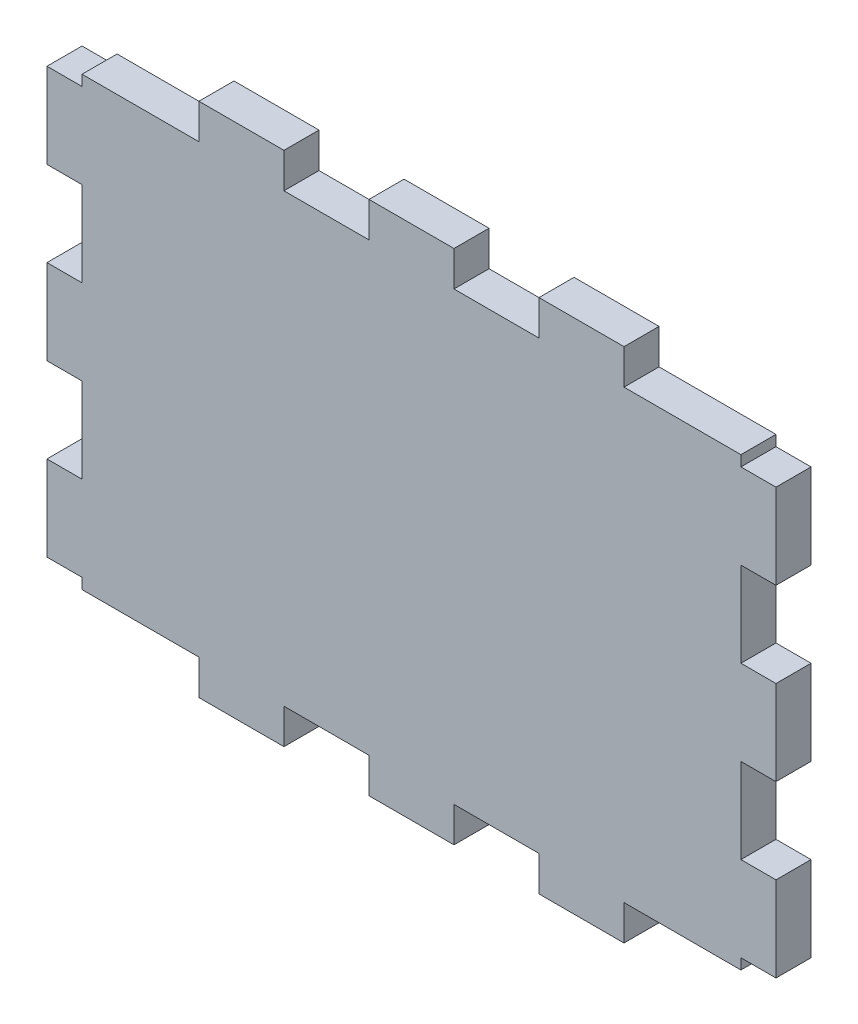
SolidWorks part; units mm, degrees
ref_plane "Plan de face" through (0, 0, 0) normal (0, 0, 1) x (1, 0, 0)
ref_plane "Plan de dessus" through (0, 0, 0) normal (0, 1, 0) x (1, 0, 0)
ref_plane "Plan de droite" through (0, 0, 0) normal (1, 0, 0) x (0, 0, -1)
sketch "Esquisse1" plane through (0, 0, 0) normal (0, 0, 1) x (1, 0, 0)
  line L1 (-31, 21) -> (31, 21)
  line L2 (-31, 21) -> (-31, -21)
  line L3 (-31, -21) -> (31, -21)
  line L4 (31, 21) -> (31, -21)
  line L5 (-31, 21) -> (31, -21) construction
  line L6 (-31, -21) -> (31, 21) construction
  point P0 (0, 0)
  dimension "D1" = 42
  dimension "D2" = 62
extrude "Boss.-Extru.1" add sketch "Esquisse1" along normal blind 3.3
sketch "Esquisse2" plane through (0, 0, 3.3) normal (0, 0, 1) x (1, 0, 0)
  line L0 (31, 21) -> (-31, 21) construction
  line L1 (-4, 24.3) -> (4, 24.3)
  line L2 (-4, 24.3) -> (-4, 21)
  line L3 (-4, 21) -> (4, 21)
  line L4 (4, 24.3) -> (4, 21)
  point P4 (0, 21)
  point P7 (0, 21)
  dimension "D1" = 8
  dimension "D2" = 3.3
extrude "Boss.-Extru.2" add sketch "Esquisse2" against normal blind 3.3
pattern_linear "Répétition linéaire1" count 2 spacing 16 along (-1, 0, 0) count 2 spacing 16 along (1, 0, 0) of "Boss.-Extru.2"
mirror "Symétrie1" about plane through (0, 0, 0) normal (0, 1, 0) of "Répétition linéaire1", "Boss.-Extru.2"
sketch "Esquisse3" plane through (0, 0, 3.3) normal (0, 0, 1) x (1, 0, 0)
  line L0 (-31, 21) -> (-31, -21) construction
  line L1 (-34.3, -4) -> (-31, -4)
  line L2 (-34.3, -4) -> (-34.3, 4)
  line L3 (-34.3, 4) -> (-31, 4)
  line L4 (-31, -4) -> (-31, 4)
  point P4 (-31, 0)
  point P7 (-31, 0)
  point P8 (-34.3, 4)
  dimension "D1" = 8
  dimension "D2" = 3.3
extrude "Boss.-Extru.3" add sketch "Esquisse3" against normal blind 3.3
pattern_linear "Répétition linéaire2" count 2 spacing 16 along (0, 1, 0) count 2 spacing 16 along (0, -1, 0) of "Boss.-Extru.3"
mirror "Symétrie2" about plane through (0, 0, 0) normal (1, 0, 0) of "Répétition linéaire2", "Boss.-Extru.3"
